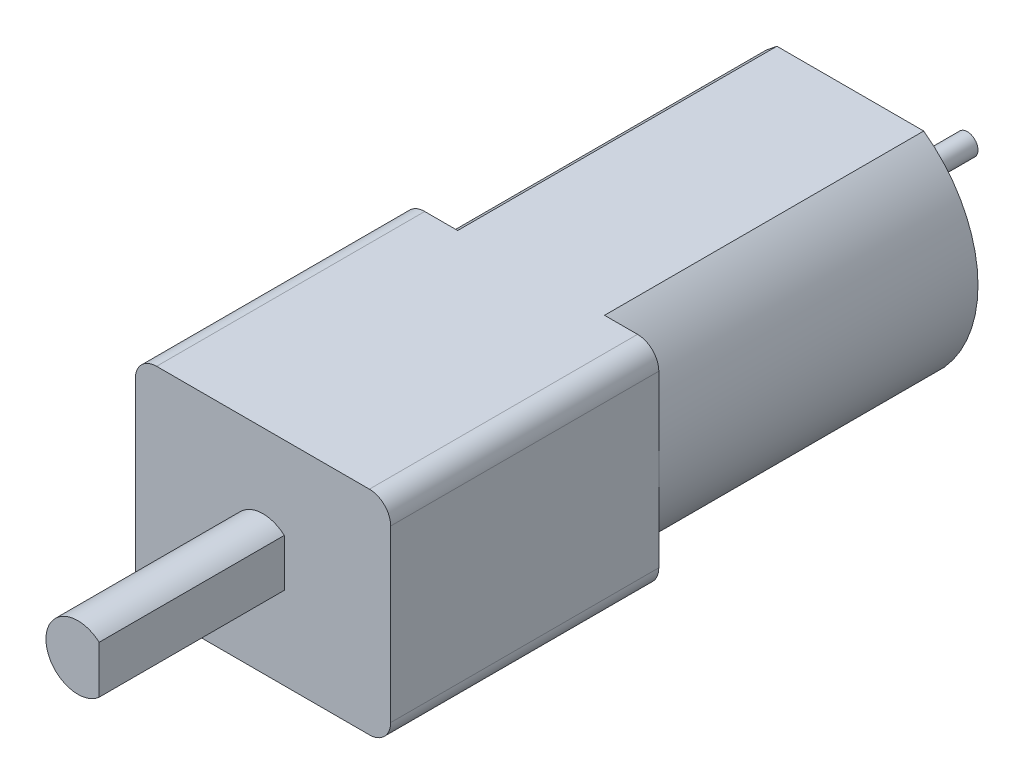
SolidWorks part; units mm, degrees
ref_plane "Front Plane" through (0, 0, 0) normal (0, 0, 1) x (1, 0, 0)
ref_plane "Top Plane" through (0, 0, 0) normal (0, 1, 0) x (1, 0, 0)
ref_plane "Right Plane" through (0, 0, 0) normal (1, 0, 0) x (0, 0, -1)
sketch "Sketch1" plane through (0, 0, 0) normal (0, 0, 1) x (1, 0, 0)
  line L1 (-3.45, 5) -> (3.45, 5)
  line L3 (-3.45, -5) -> (3.45, -5)
  line L5 (-6, 5) -> (6, -5) construction
  line L6 (-6, -5) -> (6, 5) construction
  line L11 (-3.45, 5) -> (3.45, -5) construction
  line L12 (-3.45, -5) -> (3.45, 5) construction
  arc A0 (-3.45, 5) -> (-3.45, -5) centre (0.177, 0) ccw
  arc A1 (3.45, 5) -> (3.45, -5) centre (-0.177, 0) cw
  point P0 (0, 0)
  point P6 (0, 0)
  dimension "D1" = 12
  dimension "D2" = 10
extrude "Boss-Extrude1" add sketch "Sketch1" along normal blind 15
sketch "Sketch2" plane through (0, 0, 15) normal (0, 0, 1) x (1, 0, 0)
  line L1 (-6, 5) -> (6, 5)
  line L2 (-6, 5) -> (-6, -5)
  line L3 (-6, -5) -> (6, -5)
  line L4 (6, 5) -> (6, -5)
  line L5 (-6, 5) -> (6, -5) construction
  line L6 (-6, -5) -> (6, 5) construction
  point P0 (0, 0)
  dimension "D1" = 10
  dimension "D2" = 12
extrude "Boss-Extrude2" add sketch "Sketch2" along normal blind 12.6
fillet "Fillet1" radius 1 4 edges at (6, 5, 21.3) (6, -5, 21.3) (-6, -5, 21.3) (-6, 5, 21.3)
sketch "Sketch3" plane through (0, 0, 27.6) normal (0, 0, 1) x (1, 0, 0)
  line L0 (1, 1.118) -> (1, -1.118)
  arc A0 (1, 1.118) -> (1, -1.118) centre (0, 0) ccw
  dimension "D1" = 1
  dimension "D2" = 3
extrude "Boss-Extrude3" add sketch "Sketch3" along normal blind 8.7
sketch "Sketch4" plane through (0, 0, 0) normal (0, 0, -1) x (-1, 0, 0)
  circle A0 centre (0, 0) radius 2.5
  dimension "D1" = 5
extrude "Boss-Extrude4" add sketch "Sketch4" along normal blind 1.3
sketch "Sketch5" plane through (0, 0, -1.3) normal (0, 0, -1) x (-1, 0, 0)
  circle A0 centre (0, 0) radius 0.5
extrude "Boss-Extrude5" add sketch "Sketch5" along normal blind 4.2
